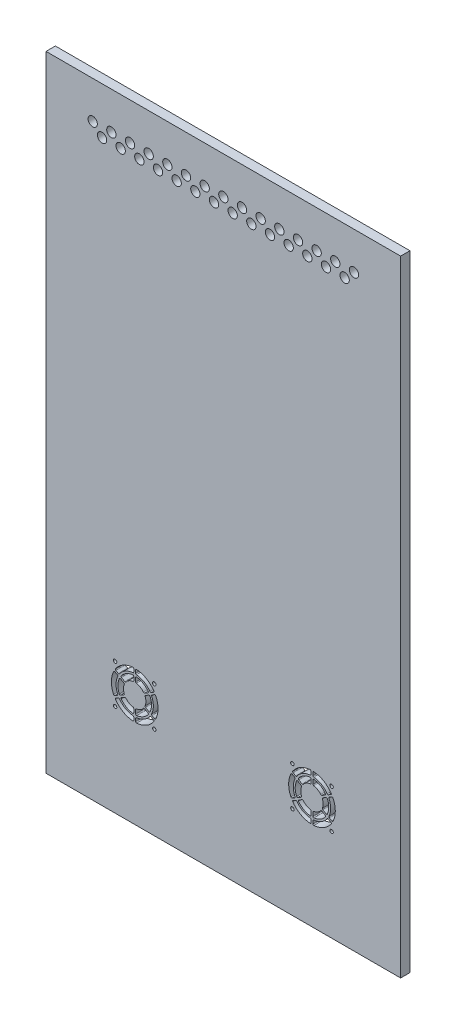
SolidWorks part; units mm, degrees
ref_plane "Plan de face" through (0, 0, 0) normal (0, 0, 1) x (1, 0, 0)
ref_plane "Plan de dessus" through (0, 0, 0) normal (0, 1, 0) x (1, 0, 0)
ref_plane "Plan de droite" through (0, 0, 0) normal (1, 0, 0) x (0, 0, -1)
sketch "Esquisse1" plane through (0, 0, 0) normal (0, 0, 1) x (1, 0, 0)
  line L1 (-190, 335) -> (190, 335)
  line L2 (-190, 335) -> (-190, -335)
  line L3 (-190, -335) -> (190, -335)
  line L4 (190, 335) -> (190, -335)
  dimension "D1" = 380
  dimension "D2" = 670
  dimension "D3" = 335
  dimension "D4" = 190
extrude "Boss.-Extru.1" add sketch "Esquisse1" along normal blind 10
sketch "Esquisse2" plane through (0, 0, 0) normal (0, 0, -1) x (-1, 0, 0)
  line L0 (-190, -170) -> (190, -170) construction
  line L1 (-190, -335) -> (-190, 335) construction
  line L2 (190, 335) -> (190, -335) construction
  line L3 (190, -335) -> (-190, -335) construction
  line L4 (-190, -190) -> (-120, -190) construction
  line L5 (0, -190) -> (0, -335) construction
  line L6 (-70, -240) -> (-70, -335) construction
  line L7 (70, -190) -> (70, -335) construction
  line L8 (-70, -190) -> (190, -190) construction
  line L9 (-70, -190) -> (-120, -190) construction
  line L10 (-70, -190) -> (-70, -240) construction
  line L11 (-70, -240) -> (-120, -240) construction
  line L12 (-120, -190) -> (-120, -240) construction
  line L13 (-120, -190) -> (-70, -240) construction
  line L14 (-76.3961, -205.4138) -> (-73.7877, -203.9078)
  line L15 (-95, -203) -> (-95, -197) construction
  line L16 (-94, -202.1548) -> (-94, -198.1181)
  line L17 (-96, -202.1548) -> (-96, -198.1181)
  line L18 (-83.3757, -209.4434) -> (-79.8798, -207.4251)
  line L21 (-84.3757, -207.7114) -> (-80.8798, -205.693)
  line L22 (-84.3757, -222.2886) -> (-80.8798, -224.307)
  line L23 (-83.3757, -220.5566) -> (-79.8798, -222.5749)
  line L24 (-96, -227.8452) -> (-96, -231.8819)
  line L25 (-94, -227.8452) -> (-94, -231.8819)
  line L26 (-106.6243, -220.5566) -> (-110.1202, -222.5749)
  line L27 (-105.6243, -222.2886) -> (-109.1202, -224.307)
  line L28 (-105.6243, -207.7114) -> (-109.1202, -205.693)
  line L29 (-106.6243, -209.4434) -> (-110.1202, -207.4251)
  line L30 (-113.6039, -224.5862) -> (-116.2123, -226.0922)
  line L31 (-112.6039, -226.3183) -> (-115.2123, -227.8243)
  line L32 (-96, -235.9045) -> (-96, -238.9165)
  line L33 (-94, -235.9045) -> (-94, -238.9165)
  line L34 (-77.3961, -226.3183) -> (-74.7877, -227.8243)
  line L35 (-76.3961, -224.5862) -> (-73.7877, -226.0922)
  line L37 (-77.3961, -203.6817) -> (-74.7877, -202.1757)
  line L38 (-94, -194.0955) -> (-94, -191.0835)
  line L39 (-96, -194.0955) -> (-96, -191.0835)
  line L40 (-112.6039, -203.6817) -> (-115.2123, -202.1757)
  line L41 (-113.6039, -205.4138) -> (-116.2123, -203.9078)
  line L42 (95, -203) -> (95, -197) construction
  line L43 (120, -190) -> (70, -240) construction
  line L44 (120, -190) -> (120, -240) construction
  line L45 (70, -240) -> (120, -240) construction
  line L46 (70, -190) -> (70, -240) construction
  line L47 (70, -190) -> (120, -190) construction
  line L48 (113.6039, -205.4138) -> (116.2123, -203.9078)
  line L49 (112.6039, -203.6817) -> (115.2123, -202.1757)
  line L50 (96, -194.0955) -> (96, -191.0835)
  line L51 (94, -194.0955) -> (94, -191.0835)
  line L52 (77.3961, -203.6817) -> (74.7877, -202.1757)
  line L53 (76.3961, -205.4138) -> (73.7877, -203.9078)
  line L54 (76.3961, -224.5862) -> (73.7877, -226.0922)
  line L55 (77.3961, -226.3183) -> (74.7877, -227.8243)
  line L56 (94, -235.9045) -> (94, -238.9165)
  line L57 (96, -235.9045) -> (96, -238.9165)
  line L58 (112.6039, -226.3183) -> (115.2123, -227.8243)
  line L59 (113.6039, -224.5862) -> (116.2123, -226.0922)
  line L60 (106.6243, -209.4434) -> (110.1202, -207.4251)
  line L61 (105.6243, -207.7114) -> (109.1202, -205.693)
  line L62 (105.6243, -222.2886) -> (109.1202, -224.307)
  line L63 (106.6243, -220.5566) -> (110.1202, -222.5749)
  line L64 (94, -227.8452) -> (94, -231.8819)
  line L65 (96, -227.8452) -> (96, -231.8819)
  line L66 (83.3757, -220.5566) -> (79.8798, -222.5749)
  line L67 (84.3757, -222.2886) -> (80.8798, -224.307)
  line L68 (84.3757, -207.7114) -> (80.8798, -205.693)
  line L69 (83.3757, -209.4434) -> (79.8798, -207.4251)
  line L70 (96, -202.1548) -> (96, -198.1181)
  line L71 (94, -202.1548) -> (94, -198.1181)
  circle A0 centre (-116, -194) radius 1.85
  circle A1 centre (-74, -194) radius 1.85
  circle A2 centre (-74, -236) radius 1.85
  circle A3 centre (-116, -236) radius 1.85
  arc A4 (-117.617, -204.3477) -> (-117.617, -225.6523) centre (-95, -215) ccw
  arc A5 (-97.0833, -190.087) -> (-115.5337, -200.7393) centre (-95, -215) ccw
  arc A6 (-74.4663, -200.7393) -> (-92.9167, -190.087) centre (-95, -215) ccw
  arc A7 (-111.2894, -226.6041) -> (-96.9048, -234.9091) centre (-95, -215) ccw
  arc A8 (-109.4214, -225.7714) -> (-97.1176, -232.875) centre (-95, -215) ccw
  arc A9 (-104.3455, -222.5274) -> (-96.8462, -226.8571) centre (-95, -215) ccw
  arc A10 (-72.383, -225.6523) -> (-72.383, -204.3477) centre (-95, -215) ccw
  arc A11 (-92.9167, -239.913) -> (-74.4663, -229.2607) centre (-95, -215) ccw
  arc A12 (-115.5337, -229.2607) -> (-97.0833, -239.913) centre (-95, -215) ccw
  arc A13 (-93.1538, -226.8571) -> (-85.6545, -222.5274) centre (-95, -215) ccw
  arc A14 (-92.8824, -232.875) -> (-80.5786, -225.7714) centre (-95, -215) ccw
  arc A15 (-93.0952, -234.9091) -> (-78.7106, -226.6041) centre (-95, -215) ccw
  arc A16 (-78.461, -222.1036) -> (-78.461, -207.8964) centre (-95, -215) ccw
  arc A17 (-76.8058, -223.305) -> (-76.8058, -206.695) centre (-95, -215) ccw
  arc A18 (-83.8083, -219.3298) -> (-83.8083, -210.6702) centre (-95, -215) ccw
  arc A19 (-85.6545, -207.4726) -> (-93.1538, -203.1429) centre (-95, -215) ccw
  arc A20 (-80.5786, -204.2286) -> (-92.8824, -197.125) centre (-95, -215) ccw
  arc A21 (-78.7106, -203.3959) -> (-93.0952, -195.0909) centre (-95, -215) ccw
  arc A22 (-96.9048, -195.0909) -> (-111.2894, -203.3959) centre (-95, -215) ccw
  arc A23 (-97.1176, -197.125) -> (-109.4214, -204.2286) centre (-95, -215) ccw
  arc A24 (-96.8462, -203.1429) -> (-104.3455, -207.4726) centre (-95, -215) ccw
  arc A25 (-113.1942, -206.695) -> (-113.1942, -223.305) centre (-95, -215) ccw
  arc A26 (-111.539, -207.8964) -> (-111.539, -222.1036) centre (-95, -215) ccw
  arc A27 (-106.1917, -210.6702) -> (-106.1917, -219.3298) centre (-95, -215) ccw
  arc A28 (-110.1202, -207.4251) -> (-111.539, -207.8964) centre (-110.6202, -208.2911) ccw
  arc A29 (-106.6243, -209.4434) -> (-106.1917, -210.6702) centre (-107.1243, -210.3094) cw
  arc A30 (-106.6243, -220.5566) -> (-106.1917, -219.3298) centre (-107.1243, -219.6906) ccw
  arc A31 (-111.539, -222.1036) -> (-110.1202, -222.5749) centre (-110.6202, -221.7089) ccw
  arc A32 (-109.4214, -225.7714) -> (-109.1202, -224.307) centre (-108.6202, -225.173) cw
  arc A33 (-105.6243, -222.2886) -> (-104.3455, -222.5274) centre (-105.1243, -223.1547) cw
  arc A34 (-96, -227.8452) -> (-96.8462, -226.8571) centre (-97, -227.8452) ccw
  arc A35 (-96, -231.8819) -> (-97.1176, -232.875) centre (-97, -231.8819) cw
  arc A36 (-92.8824, -232.875) -> (-94, -231.8819) centre (-93, -231.8819) cw
  arc A37 (-94, -227.8452) -> (-93.1538, -226.8571) centre (-93, -227.8452) cw
  arc A38 (-84.3757, -222.2886) -> (-85.6545, -222.5274) centre (-84.8757, -223.1547) ccw
  arc A39 (-80.5786, -225.7714) -> (-80.8798, -224.307) centre (-81.3798, -225.173) ccw
  arc A40 (-78.461, -222.1036) -> (-79.8798, -222.5749) centre (-79.3798, -221.7089) cw
  arc A41 (-83.3757, -220.5566) -> (-83.8083, -219.3298) centre (-82.8757, -219.6906) cw
  arc A42 (-78.461, -207.8964) -> (-79.8798, -207.4251) centre (-79.3798, -208.2911) ccw
  arc A43 (-83.3757, -209.4434) -> (-83.8083, -210.6702) centre (-82.8757, -210.3094) ccw
  arc A44 (-84.3757, -207.7114) -> (-85.6545, -207.4726) centre (-84.8757, -206.8453) cw
  arc A45 (-80.5786, -204.2286) -> (-80.8798, -205.693) centre (-81.3798, -204.827) cw
  arc A46 (-94, -198.1181) -> (-92.8824, -197.125) centre (-93, -198.1181) cw
  arc A47 (-94, -202.1548) -> (-93.1538, -203.1429) centre (-93, -202.1548) ccw
  arc A48 (-96, -202.1548) -> (-96.8462, -203.1429) centre (-97, -202.1548) cw
  arc A49 (-96, -198.1181) -> (-97.1176, -197.125) centre (-97, -198.1181) ccw
  arc A50 (-105.6243, -207.7114) -> (-104.3455, -207.4726) centre (-105.1243, -206.8453) ccw
  arc A51 (-109.1202, -205.693) -> (-109.4214, -204.2286) centre (-108.6202, -204.827) cw
  arc A52 (-115.2123, -202.1757) -> (-115.5337, -200.7393) centre (-114.7123, -201.3097) cw
  arc A53 (-111.2894, -203.3959) -> (-112.6039, -203.6817) centre (-112.1039, -202.8157) cw
  arc A54 (-113.1942, -206.695) -> (-113.6039, -205.4138) centre (-114.1039, -206.2798) ccw
  arc A55 (-116.2123, -203.9078) -> (-117.617, -204.3477) centre (-116.7123, -204.7738) ccw
  arc A56 (-116.2123, -226.0922) -> (-117.617, -225.6523) centre (-116.7123, -225.2262) cw
  arc A57 (-113.1942, -223.305) -> (-113.6039, -224.5862) centre (-114.1039, -223.7202) cw
  arc A58 (-111.2894, -226.6041) -> (-112.6039, -226.3183) centre (-112.1039, -227.1843) ccw
  arc A59 (-115.2123, -227.8243) -> (-115.5337, -229.2607) centre (-114.7123, -228.6903) ccw
  arc A60 (-96, -235.9045) -> (-96.9048, -234.9091) centre (-97, -235.9045) ccw
  arc A61 (-96, -238.9165) -> (-97.0833, -239.913) centre (-97, -238.9165) cw
  arc A62 (-94, -235.9045) -> (-93.0952, -234.9091) centre (-93, -235.9045) cw
  arc A63 (-94, -238.9165) -> (-92.9167, -239.913) centre (-93, -238.9165) ccw
  arc A64 (-74.7877, -227.8243) -> (-74.4663, -229.2607) centre (-75.2877, -228.6903) cw
  arc A65 (-77.3961, -226.3183) -> (-78.7106, -226.6041) centre (-77.8961, -227.1843) ccw
  arc A66 (-73.7877, -226.0922) -> (-72.383, -225.6523) centre (-73.2877, -225.2262) ccw
  arc A67 (-76.8058, -223.305) -> (-76.3961, -224.5862) centre (-75.8961, -223.7202) ccw
  arc A68 (-76.8058, -206.695) -> (-76.3961, -205.4138) centre (-75.8961, -206.2798) cw
  arc A69 (-73.7877, -203.9078) -> (-72.383, -204.3477) centre (-73.2877, -204.7738) cw
  arc A70 (-74.7877, -202.1757) -> (-74.4663, -200.7393) centre (-75.2877, -201.3097) ccw
  arc A71 (-78.7106, -203.3959) -> (-77.3961, -203.6817) centre (-77.8961, -202.8157) ccw
  arc A72 (-94, -191.0835) -> (-92.9167, -190.087) centre (-93, -191.0835) cw
  arc A73 (-94, -194.0955) -> (-93.0952, -195.0909) centre (-93, -194.0955) ccw
  arc A74 (-96.9048, -195.0909) -> (-96, -194.0955) centre (-97, -194.0955) ccw
  arc A75 (-96, -191.0835) -> (-97.0833, -190.087) centre (-97, -191.0835) ccw
  arc A76 (96, -191.0835) -> (97.0833, -190.087) centre (97, -191.0835) cw
  arc A77 (96.9048, -195.0909) -> (96, -194.0955) centre (97, -194.0955) cw
  arc A78 (94, -194.0955) -> (93.0952, -195.0909) centre (93, -194.0955) cw
  arc A79 (94, -191.0835) -> (92.9167, -190.087) centre (93, -191.0835) ccw
  arc A80 (78.7106, -203.3959) -> (77.3961, -203.6817) centre (77.8961, -202.8157) cw
  arc A81 (74.7877, -202.1757) -> (74.4663, -200.7393) centre (75.2877, -201.3097) cw
  arc A82 (73.7877, -203.9078) -> (72.383, -204.3477) centre (73.2877, -204.7738) ccw
  arc A83 (76.8058, -206.695) -> (76.3961, -205.4138) centre (75.8961, -206.2798) ccw
  arc A84 (76.8058, -223.305) -> (76.3961, -224.5862) centre (75.8961, -223.7202) cw
  arc A85 (73.7877, -226.0922) -> (72.383, -225.6523) centre (73.2877, -225.2262) cw
  arc A86 (77.3961, -226.3183) -> (78.7106, -226.6041) centre (77.8961, -227.1843) cw
  arc A87 (74.7877, -227.8243) -> (74.4663, -229.2607) centre (75.2877, -228.6903) ccw
  arc A88 (94, -238.9165) -> (92.9167, -239.913) centre (93, -238.9165) cw
  arc A89 (94, -235.9045) -> (93.0952, -234.9091) centre (93, -235.9045) ccw
  arc A90 (96, -238.9165) -> (97.0833, -239.913) centre (97, -238.9165) ccw
  arc A91 (96, -235.9045) -> (96.9048, -234.9091) centre (97, -235.9045) cw
  arc A92 (115.2123, -227.8243) -> (115.5337, -229.2607) centre (114.7123, -228.6903) cw
  arc A93 (111.2894, -226.6041) -> (112.6039, -226.3183) centre (112.1039, -227.1843) cw
  arc A94 (113.1942, -223.305) -> (113.6039, -224.5862) centre (114.1039, -223.7202) ccw
  arc A95 (116.2123, -226.0922) -> (117.617, -225.6523) centre (116.7123, -225.2262) ccw
  arc A96 (116.2123, -203.9078) -> (117.617, -204.3477) centre (116.7123, -204.7738) cw
  arc A97 (113.1942, -206.695) -> (113.6039, -205.4138) centre (114.1039, -206.2798) cw
  arc A98 (111.2894, -203.3959) -> (112.6039, -203.6817) centre (112.1039, -202.8157) ccw
  arc A99 (115.2123, -202.1757) -> (115.5337, -200.7393) centre (114.7123, -201.3097) ccw
  arc A100 (109.1202, -205.693) -> (109.4214, -204.2286) centre (108.6202, -204.827) ccw
  arc A101 (105.6243, -207.7114) -> (104.3455, -207.4726) centre (105.1243, -206.8453) cw
  arc A102 (96, -198.1181) -> (97.1176, -197.125) centre (97, -198.1181) cw
  arc A103 (96, -202.1548) -> (96.8462, -203.1429) centre (97, -202.1548) ccw
  arc A104 (94, -202.1548) -> (93.1538, -203.1429) centre (93, -202.1548) cw
  arc A105 (94, -198.1181) -> (92.8824, -197.125) centre (93, -198.1181) ccw
  arc A106 (80.5786, -204.2286) -> (80.8798, -205.693) centre (81.3798, -204.827) ccw
  arc A107 (84.3757, -207.7114) -> (85.6545, -207.4726) centre (84.8757, -206.8453) ccw
  arc A108 (83.3757, -209.4434) -> (83.8083, -210.6702) centre (82.8757, -210.3094) cw
  arc A109 (78.461, -207.8964) -> (79.8798, -207.4251) centre (79.3798, -208.2911) cw
  arc A110 (83.3757, -220.5566) -> (83.8083, -219.3298) centre (82.8757, -219.6906) ccw
  arc A111 (78.461, -222.1036) -> (79.8798, -222.5749) centre (79.3798, -221.7089) ccw
  arc A112 (80.5786, -225.7714) -> (80.8798, -224.307) centre (81.3798, -225.173) cw
  arc A113 (84.3757, -222.2886) -> (85.6545, -222.5274) centre (84.8757, -223.1547) cw
  arc A114 (94, -227.8452) -> (93.1538, -226.8571) centre (93, -227.8452) ccw
  arc A115 (92.8824, -232.875) -> (94, -231.8819) centre (93, -231.8819) ccw
  arc A116 (96, -231.8819) -> (97.1176, -232.875) centre (97, -231.8819) ccw
  arc A117 (96, -227.8452) -> (96.8462, -226.8571) centre (97, -227.8452) cw
  arc A118 (105.6243, -222.2886) -> (104.3455, -222.5274) centre (105.1243, -223.1547) ccw
  arc A119 (109.4214, -225.7714) -> (109.1202, -224.307) centre (108.6202, -225.173) ccw
  arc A120 (111.539, -222.1036) -> (110.1202, -222.5749) centre (110.6202, -221.7089) cw
  arc A121 (106.6243, -220.5566) -> (106.1917, -219.3298) centre (107.1243, -219.6906) cw
  arc A122 (106.6243, -209.4434) -> (106.1917, -210.6702) centre (107.1243, -210.3094) ccw
  arc A123 (110.1202, -207.4251) -> (111.539, -207.8964) centre (110.6202, -208.2911) cw
  arc A124 (106.1917, -210.6702) -> (106.1917, -219.3298) centre (95, -215) cw
  arc A125 (111.539, -207.8964) -> (111.539, -222.1036) centre (95, -215) cw
  arc A126 (113.1942, -206.695) -> (113.1942, -223.305) centre (95, -215) cw
  arc A127 (96.8462, -203.1429) -> (104.3455, -207.4726) centre (95, -215) cw
  arc A128 (97.1176, -197.125) -> (109.4214, -204.2286) centre (95, -215) cw
  arc A129 (96.9048, -195.0909) -> (111.2894, -203.3959) centre (95, -215) cw
  arc A130 (78.7106, -203.3959) -> (93.0952, -195.0909) centre (95, -215) cw
  arc A131 (80.5786, -204.2286) -> (92.8824, -197.125) centre (95, -215) cw
  arc A132 (85.6545, -207.4726) -> (93.1538, -203.1429) centre (95, -215) cw
  arc A133 (83.8083, -219.3298) -> (83.8083, -210.6702) centre (95, -215) cw
  arc A134 (76.8058, -223.305) -> (76.8058, -206.695) centre (95, -215) cw
  arc A135 (78.461, -222.1036) -> (78.461, -207.8964) centre (95, -215) cw
  arc A136 (93.0952, -234.9091) -> (78.7106, -226.6041) centre (95, -215) cw
  arc A137 (92.8824, -232.875) -> (80.5786, -225.7714) centre (95, -215) cw
  arc A138 (93.1538, -226.8571) -> (85.6545, -222.5274) centre (95, -215) cw
  arc A139 (115.5337, -229.2607) -> (97.0833, -239.913) centre (95, -215) cw
  arc A140 (92.9167, -239.913) -> (74.4663, -229.2607) centre (95, -215) cw
  arc A141 (72.383, -225.6523) -> (72.383, -204.3477) centre (95, -215) cw
  arc A142 (104.3455, -222.5274) -> (96.8462, -226.8571) centre (95, -215) cw
  arc A143 (109.4214, -225.7714) -> (97.1176, -232.875) centre (95, -215) cw
  arc A144 (111.2894, -226.6041) -> (96.9048, -234.9091) centre (95, -215) cw
  arc A145 (74.4663, -200.7393) -> (92.9167, -190.087) centre (95, -215) cw
  arc A146 (97.0833, -190.087) -> (115.5337, -200.7393) centre (95, -215) cw
  arc A147 (117.617, -204.3477) -> (117.617, -225.6523) centre (95, -215) cw
  circle A148 centre (116, -236) radius 1.85
  circle A149 centre (74, -236) radius 1.85
  circle A150 centre (74, -194) radius 1.85
  circle A151 centre (116, -194) radius 1.85
  point P34 (-34, -203)
  point P35 (-34, -197)
  point P36 (-36, -203)
  point P37 (-36, -197)
  point P65 (-35, -215)
  point P85 (-111.0644, -206.8799)
  point P124 (-94, -203.0417)
  point P127 (-96, -203.0417)
  point P130 (-96, -197.0278)
  point P139 (-111.7988, -204.1465)
  point P142 (-112.7988, -205.8785)
  point P149 (-112.7988, -224.1215)
  point P152 (-111.7988, -225.8535)
  point P161 (-94, -234.975)
  point P172 (-77.2012, -224.1215)
  point P175 (-77.2012, -205.8785)
  point P182 (-78.2012, -204.1465)
  point P189 (-96, -195.025)
  point P192 (-96, -190.02)
  point P351 (96, -190.02)
  point P352 (96, -195.025)
  point P353 (78.2012, -204.1465)
  point P354 (77.2012, -205.8785)
  point P355 (77.2012, -224.1215)
  point P356 (94, -234.975)
  point P357 (111.7988, -225.8535)
  point P358 (112.7988, -224.1215)
  point P359 (112.7988, -205.8785)
  point P360 (111.7988, -204.1465)
  point P361 (96, -197.0278)
  point P362 (96, -203.0417)
  point P363 (94, -203.0417)
  point P364 (111.0644, -206.8799)
  dimension "D1" = 50
  dimension "D2" = 50
  dimension "D5" = 42
  dimension "D6" = 42
  dimension "D7" = 42
  dimension "D8" = 42
  dimension "D9" = 4
  dimension "D3" = 70
  dimension "D4" = 20
extrude "Enlèv. mat.-Extru.1" cut sketch "Esquisse2" against normal through all
sketch "Esquisse3" plane through (0, 0, 0) normal (0, 0, -1) x (-1, 0, 0)
  line L0 (-190, 295) -> (190, 295) construction
  line L1 (-190, -335) -> (-190, 335) construction
  line L2 (190, 335) -> (190, -335) construction
  line L3 (-190, 335) -> (190, 335) construction
  line L4 (-190, 285) -> (190, 285) construction
  line L5 (-150, 335) -> (-150, 285) construction
  line L6 (150, 335) -> (150, 285) construction
  line L7 (-140, 295) -> (-140, 285) construction
  line L8 (-130, 295) -> (-130, 285) construction
  circle A0 centre (-140, 295) radius 5
  circle A1 centre (-130, 285) radius 5
  circle A2 centre (-120, 295) radius 5
  circle A3 centre (-110, 285) radius 5
  circle A4 centre (-100, 295) radius 5
  circle A5 centre (-90, 285) radius 5
  circle A6 centre (-80, 295) radius 5
  circle A7 centre (-70, 285) radius 5
  circle A8 centre (-60, 295) radius 5
  circle A9 centre (-50, 285) radius 5
  circle A10 centre (-40, 295) radius 5
  circle A11 centre (-30, 285) radius 5
  circle A12 centre (-20, 295) radius 5
  circle A13 centre (-10, 285) radius 5
  circle A14 centre (0, 295) radius 5
  circle A15 centre (10, 285) radius 5
  circle A16 centre (20, 295) radius 5
  circle A17 centre (30, 285) radius 5
  circle A18 centre (40, 295) radius 5
  circle A19 centre (50, 285) radius 5
  circle A20 centre (60, 295) radius 5
  circle A21 centre (70, 285) radius 5
  circle A22 centre (80, 295) radius 5
  circle A23 centre (90, 285) radius 5
  circle A24 centre (100, 295) radius 5
  circle A25 centre (110, 285) radius 5
  circle A26 centre (120, 295) radius 5
  circle A27 centre (130, 285) radius 5
  circle A28 centre (140, 295) radius 5
  circle A30 centre (150, 285) radius 5 [skipped]
  dimension "D7" = 15
  dimension "D1" = 40
  dimension "D2" = 10
  dimension "D3" = 40
  dimension "D4" = 40
  dimension "D5" = 10
  dimension "D6" = 10
extrude "Enlèv. mat.-Extru.2" cut sketch "Esquisse3" against normal through all
